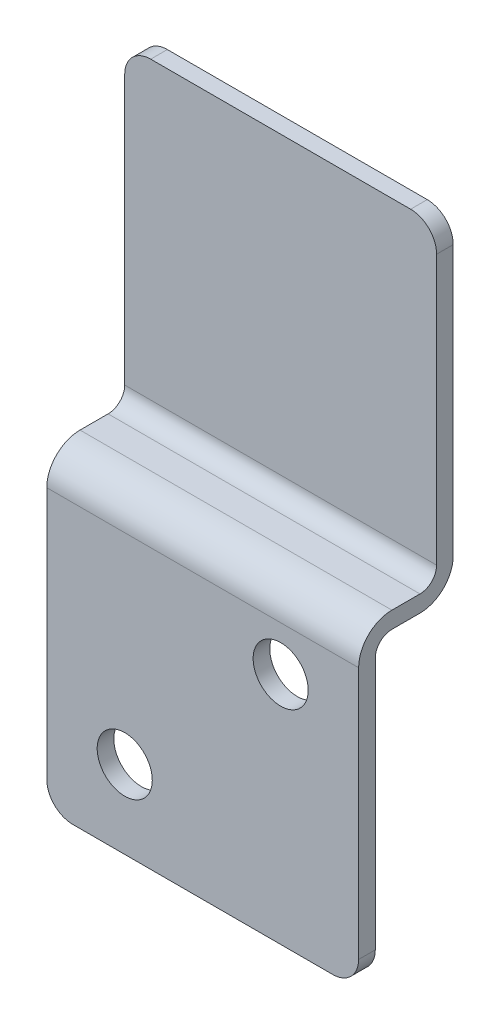
SolidWorks part; units mm, degrees
material "5052-H32"
ref_plane "Front Plane" through (0, 0, 0) normal (0, 0, 1) x (1, 0, 0)
ref_plane "Top Plane" through (0, 0, 0) normal (0, 1, 0) x (1, 0, 0)
ref_plane "Right Plane" through (0, 0, 0) normal (1, 0, 0) x (0, 0, -1)
sketch "Sketch1" plane through (0, 0, 0) normal (1, 0, 0) x (0, 0, -1)
  line L0 (0, 0) -> (0, -38.1)
  line L1 (0, -38.1) -> (-9.525, -38.1)
  line L2 (-9.525, -38.1) -> (-9.525, -76.2)
  line L3 (2.032, 0) -> (2.032, -40.132)
  line L4 (2.032, -40.132) -> (-7.493, -40.132)
  line L5 (-7.493, -40.132) -> (-7.493, -76.2)
  line L6 (-9.525, -76.2) -> (-7.493, -76.2)
  line L7 (0, 0) -> (2.032, 0)
  dimension "D1" = 2.032
  dimension "D2" = 38.1
  dimension "D3" = 76.2
  dimension "D4" = 9.525
extrude "Boss-Extrude1" add sketch "Sketch1" along normal blind 38.1
fillet "Fillet1" radius 2.032 2 edges at (19.05, -40.132, 7.493) (19.05, -38.1, 0)
fillet "Fillet2" radius 4.064 2 edges at (19.05, -38.1, 9.525) (19.05, -40.132, -2.032)
fillet "Fillet3" radius 3.175 4 edges at (0, -76.2, 8.509) (0, 0, -1.016) (38.1, -76.2, 8.509) (38.1, 0, -1.016)
sketch "Sketch2" plane through (0, 0, 9.525) normal (0, 0, 1) x (1, 0, 0)
  line L0 (34.925, -76.2) -> (3.175, -76.2) construction
  line L1 (0, -42.164) -> (0, -73.025) construction
  circle A0 centre (9.525, -66.675) radius 3.3655
  circle A1 centre (28.575, -47.625) radius 3.3655
  dimension "D1" = 9.525
  dimension "D4" = 6.731
  dimension "D2" = 9.525
  dimension "D3" = 28.575
  dimension "D5" = 28.575
extrude "Cut-Extrude1" cut sketch "Sketch2" against normal through all
